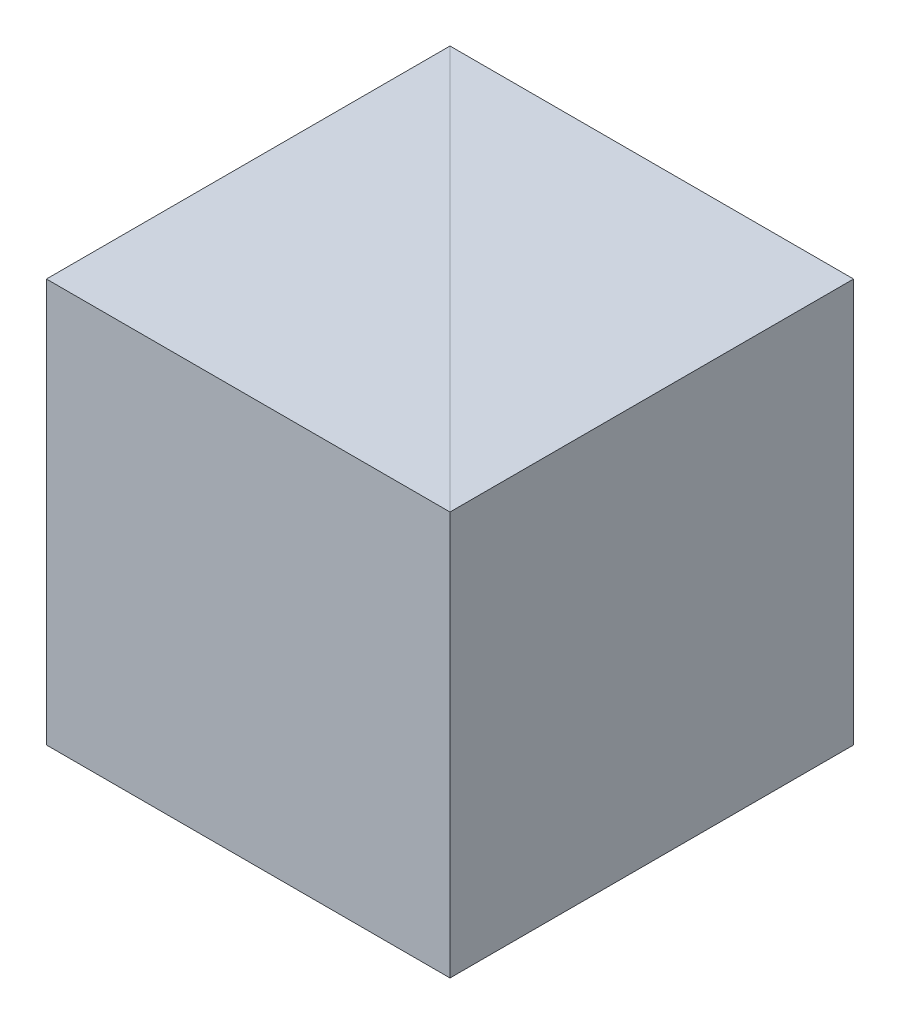
SolidWorks part; units mm, degrees
ref_plane "前视基准面" through (0, 0, 0) normal (0, 0, 1) x (1, 0, 0)
ref_plane "上视基准面" through (0, 0, 0) normal (0, 1, 0) x (1, 0, 0)
ref_plane "右视基准面" through (0, 0, 0) normal (1, 0, 0) x (0, 0, -1)
sketch "草图1" plane through (0, 0, 0) normal (0, 1, 0) x (1, 0, 0)
  line L0 (0, 0) -> (0, 5)
  line L1 (0, 5) -> (-5, 5)
  line L2 (-5, 5) -> (0, 0)
  point P4 (0, 0.2447)
  dimension "D1" = 5
  dimension "D2" = 5
extrude "凸台-拉伸1" add sketch "草图1" along normal blind 5
sketch "草图2" plane through (0, 0, 0) normal (0, -1, 0) x (1, 0, 0)
  line L0 (-5, -5) -> (-5, 0)
  line L1 (-5, 0) -> (0, 0)
  line L2 (0, 0) -> (-5, -5)
extrude "凸台-拉伸2" add sketch "草图2" against normal blind 5 separate body
